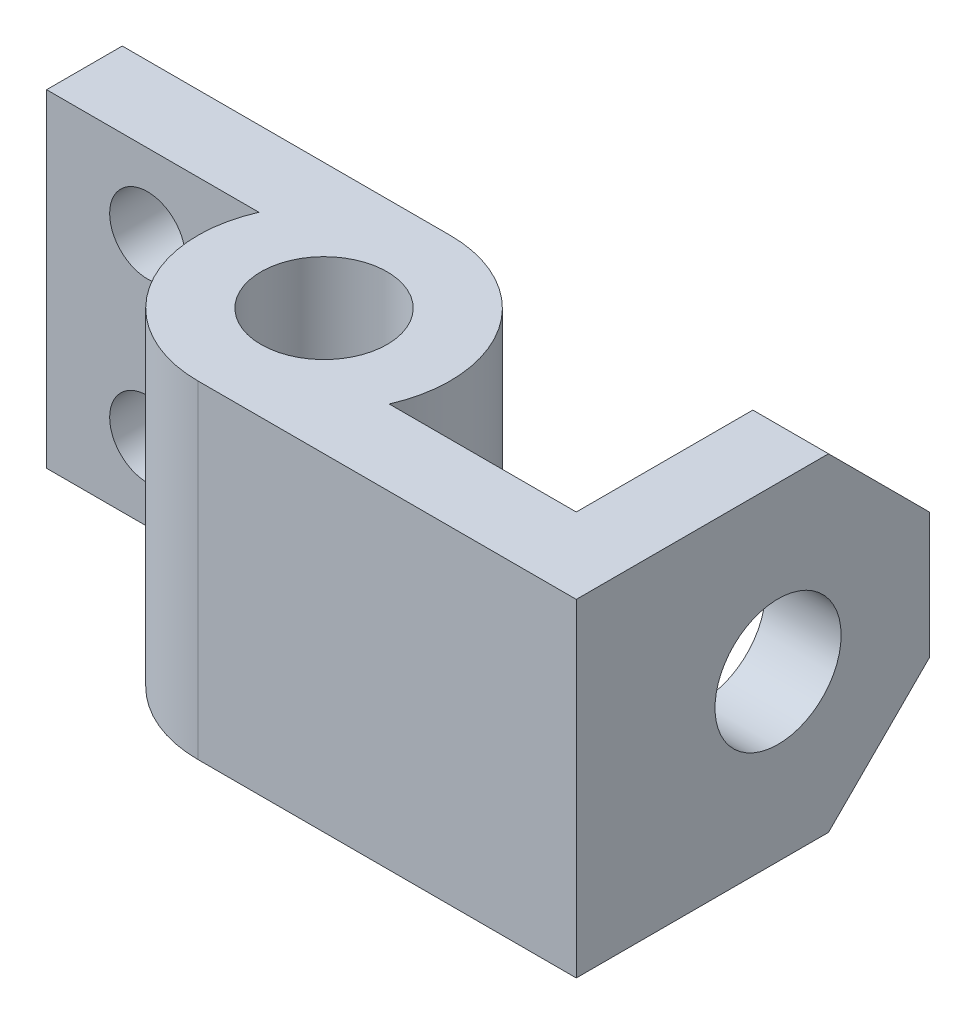
SolidWorks part; units mm, degrees
ref_plane "Front Plane" through (0, 0, 0) normal (0, 0, 1) x (1, 0, 0)
ref_plane "Top Plane" through (0, 0, 0) normal (0, 1, 0) x (1, 0, 0)
ref_plane "Right Plane" through (0, 0, 0) normal (1, 0, 0) x (0, 0, -1)
sketch "Sketch1" plane through (0, 0, 0) normal (0, 1, 0) x (1, 0, 0)
  line L0 (0, 31.75) -> (-82.55, 31.75)
  line L1 (-82.55, 31.75) -> (-82.55, 12.7)
  line L2 (-82.55, 12.7) -> (-29.0994, 12.7)
  line L3 (0, -31.75) -> (95.25, -31.75)
  line L4 (95.25, -31.75) -> (95.25, 57.15)
  line L5 (95.25, 57.15) -> (76.2, 57.15)
  line L6 (76.2, 57.15) -> (76.2, -12.7)
  line L7 (76.2, -12.7) -> (29.0994, -12.7)
  arc A0 (-29.0994, 12.7) -> (0, -31.75) centre (0, 0) ccw
  circle A1 centre (0, 0) radius 15.875
  arc A2 (29.0994, -12.7) -> (0, 31.75) centre (0, 0) ccw
  dimension "D1" = 63.5
  dimension "D2" = 31.75
  dimension "D3" = 82.55
  dimension "D4" = 19.05
  dimension "D5" = 95.25
  dimension "D6" = 88.9
  dimension "D7" = 19.05
  dimension "D8" = 19.05
extrude "Boss-Extrude1" add sketch "Sketch1" along normal blind 82.55
sketch "Sketch2" plane through (0, 0, -31.75) normal (0, 0, -1) x (-1, 0, 0)
  line L0 (82.55, 82.55) -> (82.55, 0) construction
  line L1 (0, 0) -> (82.55, 0) construction
  line L2 (0, 82.55) -> (82.55, 82.55) construction
  circle A0 centre (57.15, 63.5) radius 9.525
  circle A1 centre (57.15, 19.05) radius 9.525
  dimension "D1" = 19.05
  dimension "D2" = 25.4
  dimension "D3" = 19.05
  dimension "D4" = 19.05
  dimension "D5" = 25.4
extrude "Cut-Extrude1" cut sketch "Sketch2" against normal through all
sketch "Sketch4" plane through (95.25, 0, 0) normal (1, 0, 0) x (0, 0, -1)
  line L13 (31.75, 0) -> (57.15, 0)
  line L14 (-31.75, 0) -> (57.15, 0) construction
  line L15 (57.15, 0) -> (57.15, 25.4)
  line L16 (57.15, 82.55) -> (57.15, 0) construction
  line L17 (31.75, 0) -> (57.15, 25.4)
  line L18 (31.75, 82.55) -> (57.15, 82.55)
  line L19 (57.15, 82.55) -> (57.15, 57.15)
  line L20 (31.75, 82.55) -> (57.15, 57.15)
  dimension "D1" = 25.4
  dimension "D2" = 25.4
  dimension "D3" = 25.4
extrude "Cut-Extrude2" cut sketch "Sketch4" against normal blind 19.05
sketch "Sketch5" plane through (95.25, 0, 0) normal (1, 0, 0) x (0, 0, -1)
  line L0 (-31.75, 0) -> (31.75, 0) construction
  line L1 (-31.75, 82.55) -> (-31.75, 0) construction
  circle A0 centre (19.05, 41.402) radius 15.875
  dimension "D1" = 31.75
  dimension "D2" = 41.402
  dimension "D3" = 50.8
extrude "Cut-Extrude3" cut sketch "Sketch5" against normal blind 19.05
